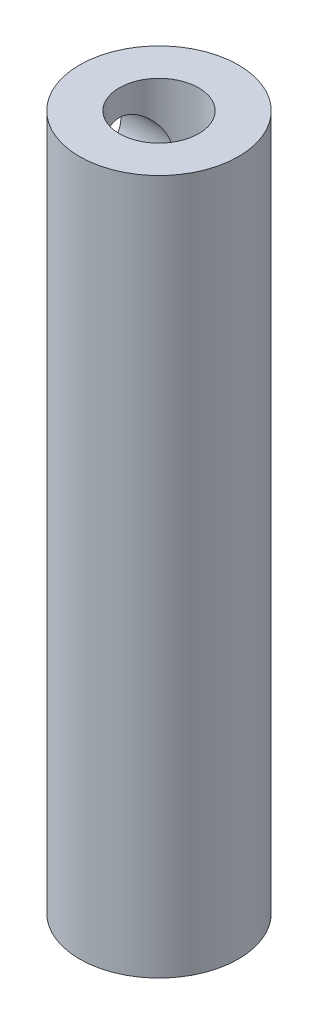
SolidWorks part; units mm, degrees
ref_plane "Alzado" through (0, 0, 0) normal (0, 0, 1) x (1, 0, 0)
ref_plane "Planta" through (0, 0, 0) normal (0, 1, 0) x (1, 0, 0)
ref_plane "Vista lateral" through (0, 0, 0) normal (1, 0, 0) x (0, 0, -1)
sketch "Croquis1" plane through (0, 0, 0) normal (0, 1, 0) x (1, 0, 0)
  circle A0 centre (0, 0) radius 4
  dimension "D1" = 8
extrude "Saliente-Extruir1" add sketch "Croquis1" along normal blind 35
sketch "Croquis2" plane through (0, 35, 0) normal (0, 1, 0) x (1, 0, 0)
  circle A0 centre (0, 0) radius 2
  dimension "D1" = 4
extrude "Cortar-Extruir1" cut sketch "Croquis2" against normal blind 10
hole_wizard "Taladro de margen para M31" positions "Croquis3D2" profile "Croquis3" hole size "M3" standard "Ansi Metric"
sketch3d "Croquis3D2"
  point P0 (-4, 32, 0)
  dimension "D1" = 32
  dimension "D2" = 0
sketch "Croquis3" plane through (-4, 32, 0) normal (0, 1, 0) x (0, 0, 1)
  line L0 (0, 0) -> (0, 4.0215)
  line L1 (0, 4.0215) -> (1.7, 3)
  line L2 (1.7, 3) -> (1.7, 0)
  line L5 (1.7, 0) -> (0, 0)
  line L10 (0, 4.0215) -> (-1.7, 3) construction
  line L11 (0, -6.35) -> (0, 107.95) construction
  dimension "Diámetro de taladro" = 3.4
  dimension "Profundidad de taladro" = 3
  dimension "Ángulo de perforador" = 118
